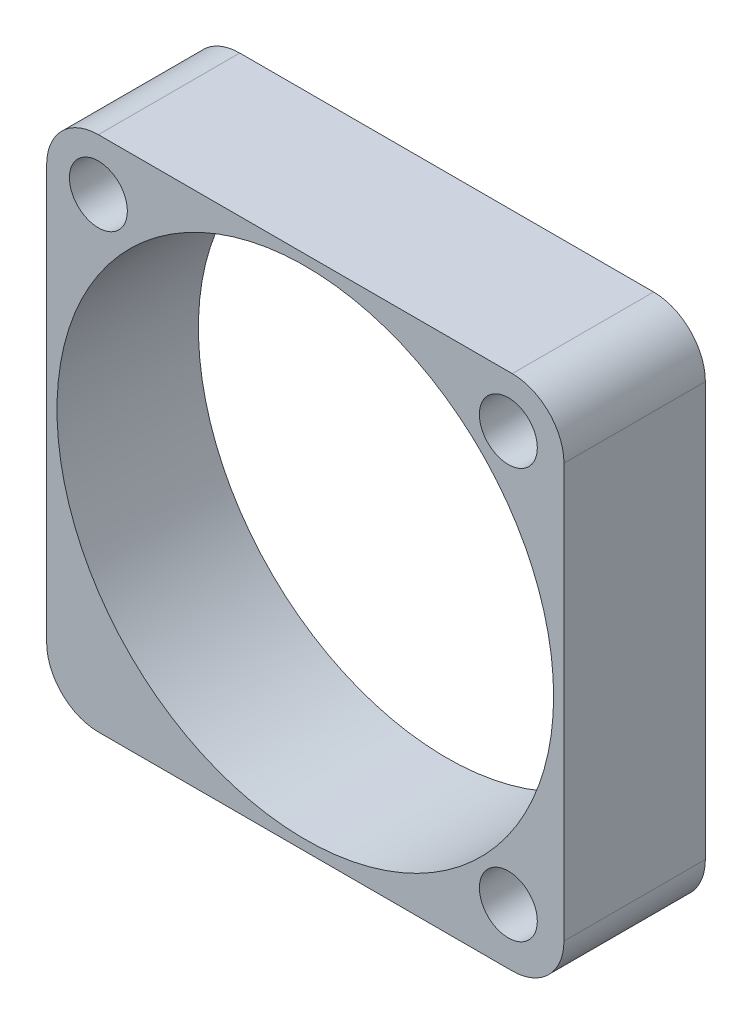
SolidWorks part; units mm, degrees
ref_plane "Front Plane" through (0, 0, 0) normal (0, 0, 1) x (1, 0, 0)
ref_plane "Top Plane" through (0, 0, 0) normal (0, 1, 0) x (1, 0, 0)
ref_plane "Right Plane" through (0, 0, 0) normal (1, 0, 0) x (0, 0, -1)
sketch "Sketch1" plane through (0, 0, 0) normal (0, 0, 1) x (1, 0, 0)
  line L1 (0, 0) -> (25, 0)
  line L2 (0, 0) -> (0, 25)
  line L3 (0, 25) -> (25, 25)
  line L4 (25, 0) -> (25, 25)
  dimension "D1" = 25
extrude "Boss-Extrude1" add sketch "Sketch1" along normal blind 6.8325
sketch "Sketch2" plane through (0, 0, 6.8325) normal (0, 0, 1) x (1, 0, 0)
  line L0 (12.5, 25) -> (12.5, 0) construction
  line L1 (25, 25) -> (0, 25) construction
  line L2 (0, 0) -> (25, 0) construction
  line L3 (0, 12.5) -> (25, 12.5) construction
  line L4 (0, 25) -> (0, 0) construction
  line L5 (25, 0) -> (25, 25) construction
  circle A0 centre (12.5, 12.5) radius 12
  dimension "D1" = 24
extrude "Cut-Extrude1" cut sketch "Sketch2" against normal through all
sketch "Sketch3" plane through (0, 0, 6.8325) normal (0, 0, 1) x (1, 0, 0)
  line L0 (12.5, 25) -> (12.5, 0) construction
  line L1 (25, 25) -> (0, 25) construction
  line L2 (0, 0) -> (25, 0) construction
  line L3 (2.5, 22.5) -> (12.5, 22.5) construction
  line L4 (0, 12.5) -> (25, 12.5) construction
  line L5 (0, 25) -> (0, 0) construction
  line L6 (25, 0) -> (25, 25) construction
  line L7 (2.5, 22.5) -> (2.5, 12.5) construction
  line L8 (12.406, 12.594) -> (2.5, 22.5) construction
  line L9 (12.406, 12.594) -> (22.312, 22.5) construction
  circle A0 centre (2.5, 22.5) radius 1.4
  circle A1 centre (22.312, 22.5) radius 1.4
  circle A2 centre (22.312, 2.688) radius 1.4
  point P15 (12.5, 12.5)
  dimension "D1" = 2.8
  dimension "D2" = 10
  dimension "D4" = 90
  dimension "D3" = 3
extrude "Cut-Extrude2" cut sketch "Sketch3" against normal through all
fillet "Fillet1" radius 2.5 4 edges at (0, 25, 3.4162) (0, 0, 3.4162) (25, 0, 3.4162) (25, 25, 3.4162)
